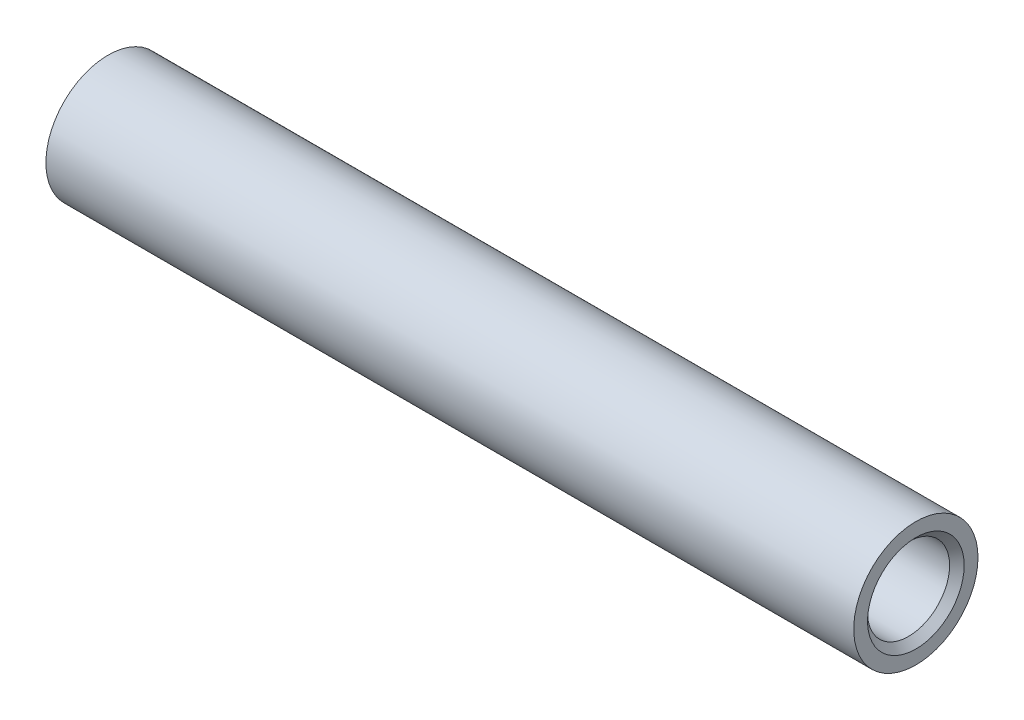
SolidWorks part; units mm, degrees
ref_plane "前视基准面" through (0, 0, 0) normal (0, 0, 1) x (1, 0, 0)
ref_plane "上视基准面" through (0, 0, 0) normal (0, 1, 0) x (1, 0, 0)
ref_plane "右视基准面" through (0, 0, 0) normal (1, 0, 0) x (0, 0, -1)
sketch "草图1" plane through (0, 0, 0) normal (1, 0, 0) x (0, 0, -1)
  circle A0 centre (0, 0) radius 5
extrude "凸台-拉伸2" add sketch "草图1" along normal blind 65 contours A0
hole_wizard "G1/16 螺纹孔1" positions "草图3" profile "草图4" tap size "G1/16" standard "GB"
sketch "草图3" plane through (0, 0, 0) normal (-1, 0, 0) x (0, 0, 1)
  point P0 (0, 0)
sketch "草图4" plane through (0, 0, 0) normal (0, 1, 0) x (0, 0, 1)
  line L0 (0, 0) -> (0, 21.9828)
  line L1 (0, 21.9828) -> (3.3, 20)
  line L2 (3.3, 20) -> (3.3, 0.5865)
  line L3 (3.3, 0.5865) -> (3.8865, 0)
  line L5 (3.8865, 0) -> (0, 0)
  line L6 (-3.3, 0.5865) -> (-3.8865, 0) construction
  line L10 (0, 21.9828) -> (-3.3, 20) construction
  line L11 (0, -6.35) -> (0, 107.95) construction
  dimension "螺纹孔钻头直径" = 6.6
  dimension "螺纹孔钻头深度" = 20
  dimension "近端锥形沉头孔直径" = 7.773
  dimension "近端锥形沉头孔角度" = 90
  dimension "导头角度" = 118
cosmetic thread "孔螺蚊线1" parameters "D1"=15.45, "D2"=7.723
hole_wizard "G1/16 螺纹孔2" positions "草图5" profile "草图6" tap size "G1/16" standard "GB"
sketch "草图5" plane through (65, 0, 0) normal (1, 0, 0) x (0, 0, -1)
  point P0 (0, 0)
sketch "草图6" plane through (65, 0, 0) normal (0, 1, 0) x (0, 0, -1)
  line L0 (0, 0) -> (0, 21.9828)
  line L1 (0, 21.9828) -> (3.3, 20)
  line L2 (3.3, 20) -> (3.3, 0.5865)
  line L3 (3.3, 0.5865) -> (3.8865, 0)
  line L5 (3.8865, 0) -> (0, 0)
  line L6 (-3.3, 0.5865) -> (-3.8865, 0) construction
  line L10 (0, 21.9828) -> (-3.3, 20) construction
  line L11 (0, -6.35) -> (0, 107.95) construction
  dimension "螺纹孔钻头直径" = 6.6
  dimension "螺纹孔钻头深度" = 20
  dimension "近端锥形沉头孔直径" = 7.773
  dimension "近端锥形沉头孔角度" = 90
  dimension "导头角度" = 118
cosmetic thread "孔螺蚊线2" parameters "D1"=15.45, "D2"=7.723
